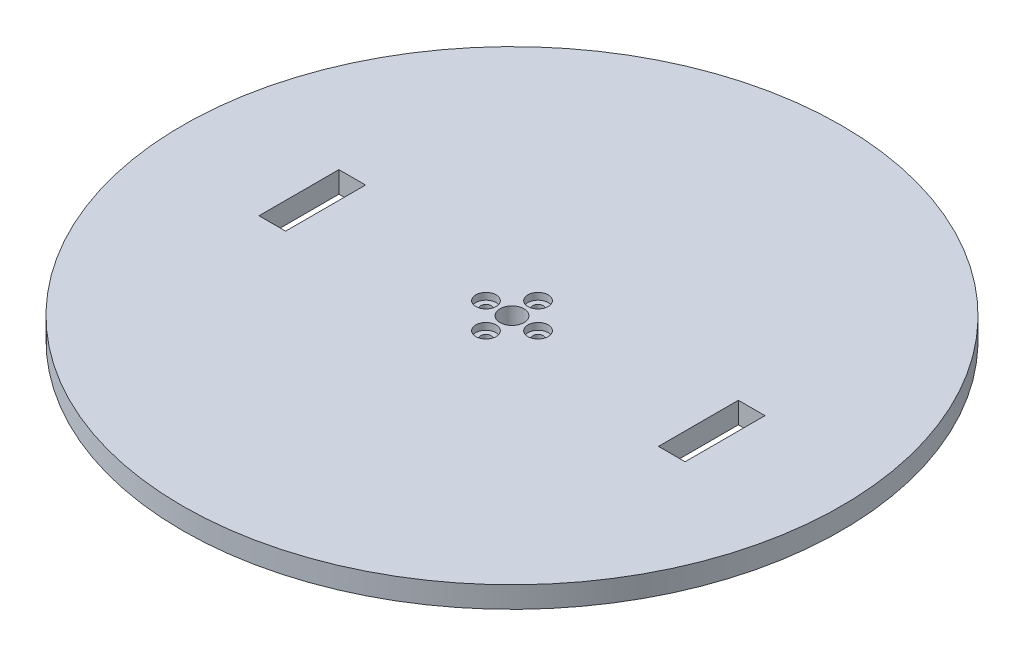
SolidWorks part; units mm, degrees
material "ABS"
ref_plane "Front Plane" through (0, 0, 0) normal (0, 0, 1) x (1, 0, 0)
ref_plane "Top Plane" through (0, 0, 0) normal (0, 1, 0) x (1, 0, 0)
ref_plane "Right Plane" through (0, 0, 0) normal (1, 0, 0) x (0, 0, -1)
sketch "Sketch1" plane through (0, 0, 0) normal (0, 1, 0) x (1, 0, 0)
  circle A0 centre (0, 0) radius 123.75
  dimension "D1" = 247.5
extrude "Boss-Extrude1" add sketch "Sketch1" along normal blind 8
sketch "Sketch2" plane through (0, 8, 0) normal (0, 1, 0) x (1, 0, 0)
  circle A0 centre (0, 0) radius 9.779
  circle A1 centre (0, 9.779) radius 1.905
  dimension "D1" = 19.558
  dimension "D2" = 3.81
extrude "Cut-Extrude2" cut sketch "Sketch2" against normal through all contours A0 A1 | A0 A1
pattern_circular "CirPattern1" count 4 every 90 about axis through (0, 0, 0) along (0, 1, 0) of "Cut-Extrude2"
sketch "Sketch3" plane through (0, 8, 0) normal (0, 1, 0) x (1, 0, 0)
  circle A0 centre (0, 0) radius 4.5
  dimension "D1" = 9
extrude "Cut-Extrude3" cut sketch "Sketch3" against normal through all
sketch "Sketch4" plane through (0, 8, 0) normal (0, 1, 0) x (1, 0, 0)
  circle A0 centre (0, 9.779) radius 3.81
  dimension "D1" = 7.62
extrude "Cut-Extrude4" cut sketch "Sketch4" against normal blind 2.54
pattern_circular "CirPattern2" count 4 every 90 about axis through (0, 0, 0) along (0, 1, 0) of "Cut-Extrude4"
sketch "Sketch5" plane through (0, 8, 0) normal (0, 1, 0) x (1, 0, 0)
  line L0 (0, -123.75) -> (0, 123.75) construction
  line L1 (123.75, 0) -> (-123.75, 0) construction
  line L2 (80, -15) -> (70, -15)
  line L3 (80, -15) -> (80, 15)
  line L4 (80, 15) -> (70, 15)
  line L5 (70, -15) -> (70, 15)
  line L6 (-80, 15) -> (-70, 15)
  line L7 (-70, -15) -> (-70, 15)
  line L8 (-80, -15) -> (-70, -15)
  line L9 (-80, -15) -> (-80, 15)
  circle A0 centre (0, 0) radius 123.75 construction
  dimension "D1" = 10
  dimension "D2" = 30
  dimension "D3" = 15
  dimension "D4" = 70
extrude "Cut-Extrude5" cut sketch "Sketch5" against normal through all
